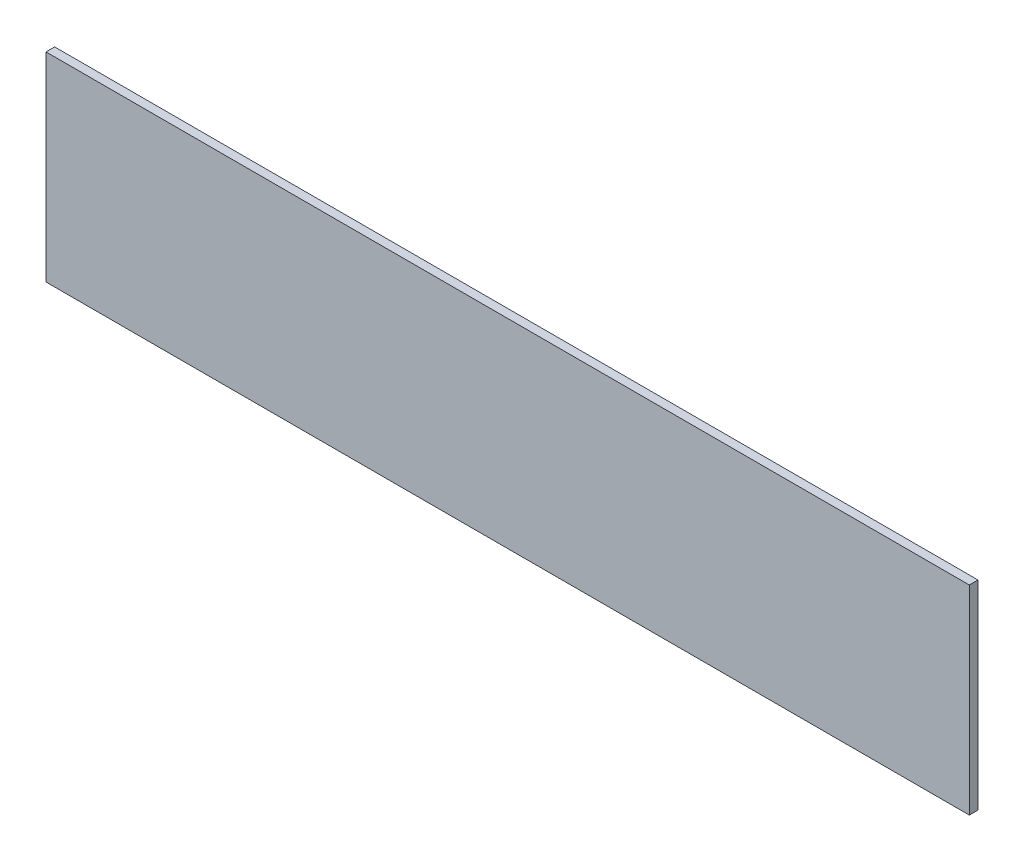
SolidWorks part; units mm, degrees
ref_plane "Front" through (0, 0, 0) normal (0, 0, 1) x (1, 0, 0)
ref_plane "Top" through (0, 0, 0) normal (0, 1, 0) x (1, 0, 0)
ref_plane "Right" through (0, 0, 0) normal (1, 0, 0) x (0, 0, -1)
sketch "Sketch1" plane through (0, 0, 0) normal (0, 0, 1) x (1, 0, 0)
  line L0 (341.5, 76.2) -> (341.5, 0) construction
  line L1 (341.5, 0) -> (0, 0) construction
  line L2 (0, 76.2) -> (0, 0) construction
  line L3 (341.5, 76.2) -> (0, 76.2) construction
  line L4 (341.5, 76.2) -> (341.5, 0) construction
  line L5 (341.5, 0) -> (0, 0) construction
  line L6 (0, 76.2) -> (0, 0) construction
  line L7 (341.5, 76.2) -> (0, 76.2) construction
  line L9 (1.5875, 76.2) -> (339.9125, 76.2)
  line L10 (1.5875, 76.2) -> (1.5875, 3.175)
  line L11 (1.5875, 3.175) -> (339.9125, 3.175)
  line L12 (339.9125, 76.2) -> (339.9125, 3.175)
  point P8 (170.75, 76.2)
  dimension "D1" = 1.5875
  dimension "D2" = 3.175
extrude "Boss-Extrude1" add sketch "Sketch1" against normal blind 3.175
sketch "Sketch2" plane through (0, 0, 0) normal (0, 0, 1) x (1, 0, 0)
  line L0 (148.25, 58.6875) -> (148.25, 20.6875) construction
  line L1 (148.25, 20.6875) -> (193.25, 20.6875) construction
  line L2 (193.25, 20.6875) -> (193.25, 58.6875) construction
  line L3 (193.25, 58.6875) -> (170.75, 58.6875) construction
  line L4 (170.75, 58.6875) -> (148.25, 58.6875) construction
  line L5 (148.25, 39.6875) -> (33.95, 39.6875) construction
  line L6 (148.25, 39.6875) -> (193.25, 39.6875) construction
  line L8 (193.25, 39.6875) -> (294.85, 39.6875)
  line L12 (339.9125, 76.2) -> (1.5875, 76.2)
  line L13 (339.9125, 3.175) -> (339.9125, 76.2)
  line L14 (1.5875, 3.175) -> (339.9125, 3.175)
  line L15 (1.5875, 76.2) -> (1.5875, 3.175)
  line L16 (339.9125, 76.2) -> (1.5875, 76.2)
  line L17 (339.9125, 3.175) -> (339.9125, 76.2)
  line L18 (1.5875, 3.175) -> (339.9125, 3.175)
  line L19 (1.5875, 76.2) -> (1.5875, 3.175)
  point P6 (170.75, 20.6875)
  point P8 (65.7, 39.6875)
  point P9 (1.5875, 39.6875)
  point P10 (170.75, 76.2)
  point P13 (97.45, 39.6875)
  point P17 (244.05, 39.6875)
  dimension "D2" = 38
  dimension "D3" = 45
  dimension "D4" = 114.3
  dimension "D5" = 50.8
  dimension "D6" = 31.75
  dimension "D7" = 50.8
  dimension "D8" = 50.8
equation "\"D1@Sketch1\"=\"acc side wall thickness@FS2-EN-ACC-A-0003-V1, ACCUMULATOR CONTAINER.Assembly\"/2"
equation "\"D2@Sketch1\"=\"acc bottom wall thickness@FS2-EN-ACC-A-0003-V1, ACCUMULATOR CONTAINER.Assembly\"/2"
equation "\"D2@Sketch2\"=\"GFC Vertical C2C@FS2-EN-ACC-A-0001-V1, FULL ACCUMULATOR ASSEMBLY.Assembly\""
equation "\"D3@Sketch2\"=\"GFC Horizontal C2C@FS2-EN-ACC-A-0001-V1, FULL ACCUMULATOR ASSEMBLY.Assembly\""
